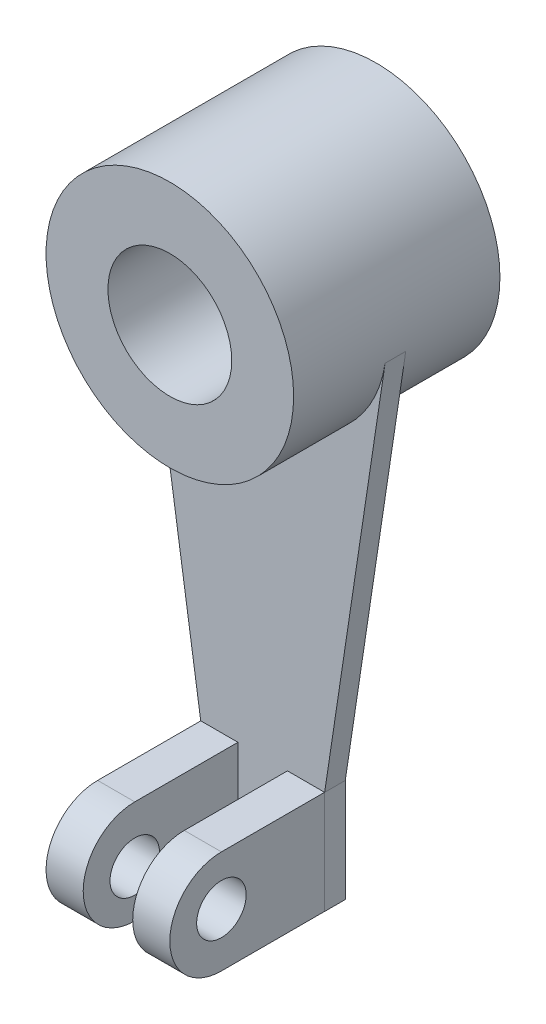
SolidWorks part; units mm, degrees
ref_plane "Front Plane" through (0, 0, 0) normal (0, 0, 1) x (1, 0, 0)
ref_plane "Top Plane" through (0, 0, 0) normal (0, 1, 0) x (1, 0, 0)
ref_plane "Right Plane" through (0, 0, 0) normal (1, 0, 0) x (0, 0, -1)
sketch "Sketch1" plane through (0, 0, 0) normal (0, 0, 1) x (1, 0, 0)
  circle A0 centre (0, 0) radius 30
  dimension "D1" = 60
extrude "Boss-Extrude1" add sketch "Sketch1" along normal mid plane 50
sketch "Sketch2" plane through (0, 0, 25) normal (0, 0, 1) x (1, 0, 0)
  circle A0 centre (0, 0) radius 15
  dimension "D1" = 30
extrude "Cut-Extrude1" cut sketch "Sketch2" against normal blind 50
sketch "Sketch5" plane through (0, 0, 0) normal (0, 0, 1) x (1, 0, 0)
  line L0 (0, -126.8488) -> (0, 90.8621) construction
  line L1 (0, -126.8488) -> (15, -126.8488)
  line L2 (15, -126.8488) -> (15, -101.8488)
  line L3 (15, -101.8488) -> (29.6655, -4.4676)
  line L4 (0, -126.8488) -> (-15.0191, -126.8488)
  line L5 (-15.0191, -126.8488) -> (-15.0191, -101.8517)
  line L6 (-15.0191, -101.8517) -> (-29.6664, -4.4618)
  circle A0 centre (0, 0) radius 30 construction
  arc A1 (-29.6664, -4.4618) -> (29.6655, -4.4676) centre (0, 0) ccw
  dimension "D1" = 25
  dimension "D2" = 30
extrude "Boss-Extrude2" add sketch "Sketch5" along normal mid plane 5
sketch "Sketch7" plane through (15, 0, 0) normal (1, 0, 0) x (0, 0, -1)
  line L0 (-2.5, -101.8488) -> (-27.5, -101.8488)
  line L2 (-27.5, -126.8488) -> (-2.5, -126.8488)
  line L3 (-2.5, -126.8488) -> (-2.5, -101.8488)
  arc A0 (-27.5, -101.8488) -> (-27.5, -126.8488) centre (-27.5, -114.3488) ccw
  dimension "D2" = 12.5
  dimension "D1" = 25
extrude "Boss-Extrude5" add sketch "Sketch7" against normal blind 9
hole_wizard "Ø12.0mm Dowel Hole2" positions "Sketch13" profile "Sketch12" hole size "Ø12.0" standard "ANSI Metric"
sketch "Sketch13" plane through (15, 0, 0) normal (1, 0, 0) x (0, 0, -1)
  point P0 (-27.5, -113.8488)
  dimension "D1" = 12
  dimension "D2" = 25
sketch "Sketch12" plane through (15, -113.8488, 27.5) normal (0, 1, 0) x (0, 0, -1)
  line L0 (0, 0) -> (0, 12.6042)
  line L1 (0, 12.6042) -> (6, 8.999)
  line L2 (6, 8.999) -> (6, 0)
  line L5 (6, 0) -> (0, 0)
  line L10 (0, 12.6042) -> (-6, 8.999) construction
  line L11 (0, -6.35) -> (0, 107.95) construction
  dimension "Hole Dia." = 12
  dimension "Hole Depth" = 8.999
  dimension "Drill Angle" = 118
mirror "Mirror1" about plane through (0, 0, 0) normal (1, 0, 0) of "Boss-Extrude2", "Boss-Extrude5"
hole_wizard "Ø12.0mm Dowel Hole4" positions "Sketch19" profile "Sketch18" hole size "Ø12.0" standard "ANSI Metric"
sketch "Sketch19" plane through (-15, 0, 0) normal (-1, 0, 0) x (0, 0, 1)
  arc A0 (27.5, -126.8488) -> (27.5, -101.8488) centre (27.5, -114.3488) ccw construction
  point P0 (27.5, -115.4211)
  point P3 (40, -114.3488)
  dimension "D1" = 12.5
sketch "Sketch18" plane through (-15, -115.4211, 27.5) normal (0, 1, 0) x (0, 0, 1)
  line L0 (0, 0) -> (0, 12.6042)
  line L1 (0, 12.6042) -> (6, 8.999)
  line L2 (6, 8.999) -> (6, 0)
  line L5 (6, 0) -> (0, 0)
  line L10 (0, 12.6042) -> (-6, 8.999) construction
  line L11 (0, -6.35) -> (0, 107.95) construction
  dimension "Hole Dia." = 12
  dimension "Hole Depth" = 8.999
  dimension "Drill Angle" = 118
